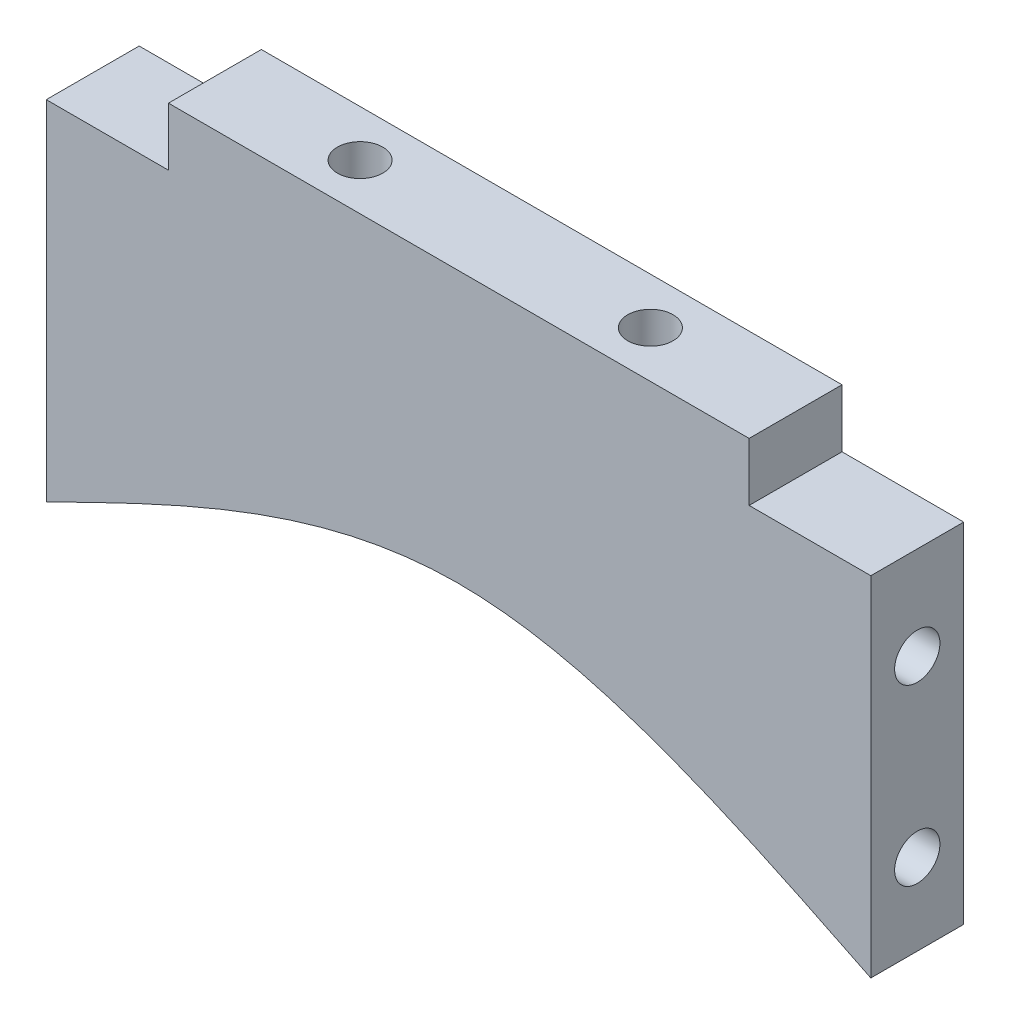
SolidWorks part; units mm, degrees
ref_plane "Front Plane" through (0, 0, 0) normal (0, 0, 1) x (1, 0, 0)
ref_plane "Top Plane" through (0, 0, 0) normal (0, 1, 0) x (1, 0, 0)
ref_plane "Right Plane" through (0, 0, 0) normal (1, 0, 0) x (0, 0, -1)
sketch "Sketch1" plane through (0, 0, 0) normal (0, 0, 1) x (1, 0, 0)
  line L0 (-10.2785, -19.1552) -> (-10.2577, 15.8448) construction
  line L1 (-45.7785, 10.8448) -> (-35.2577, 10.8448)
  line L2 (-45.7785, 10.8448) -> (-45.7785, -19.1552)
  line L3 (-45.7785, -19.1552) -> (25.2215, -19.1552)
  line L4 (25.2215, 10.8448) -> (25.2215, -19.1552)
  line L6 (14.7423, 10.8448) -> (14.7423, 15.8448)
  line L7 (14.7423, 15.8448) -> (-35.2577, 15.8448)
  line L8 (-35.2577, 10.8448) -> (-35.2577, 15.8448)
  line L9 (14.7423, 10.8448) -> (25.2215, 10.8448)
  dimension "D1" = 71
  dimension "D2" = 30
  dimension "D3" = 5
  dimension "D4" = 50
extrude "Extrude1" add sketch "Sketch1" along normal blind 8
sketch "Sketch2" plane through (0, 0, 8) normal (0, 0, 1) x (1, 0, 0)
  line L0 (-10.2577, 15.8448) -> (-10.2785, -19.1552) construction
  line L1 (14.7423, 15.8448) -> (-35.2577, 15.8448) construction
  line L2 (-45.7785, -19.1552) -> (25.2215, -19.1552) construction
  line L3 (-45.7785, -19.1552) -> (25.2215, -19.1552)
  spline S0 degree 3 poles (-45.7785, -19.1552) (-33.9427, -13.3188) (-10.2754, -1.6481) (13.3906, -13.3202) (25.2215, -19.1552) knots 0 0 0 0 0.500088 1 1 1 1
extrude "Extrude2" cut sketch "Sketch2" against normal blind 8
sketch "Sketch3" plane through (0, 15.8448, 0) normal (0, 1, 0) x (-1, 0, 0)
  line L0 (35.2577, 4) -> (-14.7423, 4) construction
  line L1 (35.2577, 8) -> (35.2577, 0) construction
  line L2 (-14.7423, 8) -> (-14.7423, 0) construction
  circle A0 centre (22.7577, 4) radius 1.95
  circle A1 centre (-2.2423, 4) radius 1.95
  dimension "D1" = 3.9
  dimension "D2" = 25
  dimension "D3" = 12.5
  dimension "D4" = 12.5
extrude "Extrude3" cut sketch "Sketch3" against normal blind 15
sketch "Sketch4" plane through (25.2215, 0, 0) normal (1, 0, 0) x (0, 0, -1)
  line L0 (-4, 10.8448) -> (-4, -19.1552) construction
  line L1 (-8, 10.8448) -> (0, 10.8448) construction
  line L2 (-8, -19.1552) -> (0, -19.1552) construction
  circle A0 centre (-4, 2.8448) radius 1.95
  circle A1 centre (-4, -12.1552) radius 1.95
  dimension "D1" = 3.9
  dimension "D2" = 15
  dimension "D3" = 8
extrude "Extrude4" cut sketch "Sketch4" against normal blind 10
sketch "Sketch5" plane through (-45.7785, 0, 0) normal (-1, 0, 0) x (0, 0, 1)
  circle A0 centre (4, 2.8448) radius 1.95
  circle A1 centre (4, -12.1552) radius 1.95
  circle A2 centre (4, 2.8448) radius 1.95 construction
  circle A3 centre (4, -12.1552) radius 1.95 construction
extrude "Extrude5" cut sketch "Sketch5" against normal blind 10
